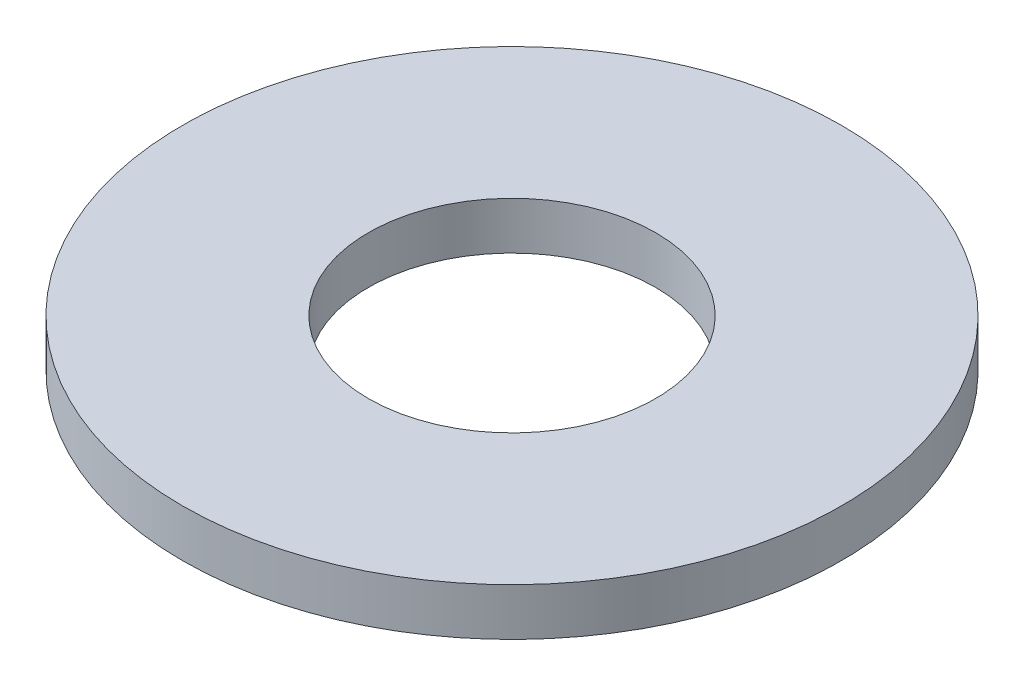
SolidWorks part; units mm, degrees
ref_plane "Front Plane" through (0, 0, 0) normal (0, 0, 1) x (1, 0, 0)
ref_plane "Top Plane" through (0, 0, 0) normal (0, 1, 0) x (1, 0, 0)
ref_plane "Right Plane" through (0, 0, 0) normal (1, 0, 0) x (0, 0, -1)
sketch "Sketch1" plane through (0, 0, 0) normal (0, 1, 0) x (1, 0, 0)
  circle A0 centre (0, 0) radius 3.175
  dimension "OD" = 6.35
extrude "Boss-Extrude1" add sketch "Sketch1" along normal blind 0.4572
sketch "Sketch5" plane through (0, 0.4572, 0) normal (0, 1, 0) x (-1, 0, 0)
  circle A0 centre (0, 0) radius 1.3843
  dimension "ID" = 2.7686
extrude "Cut-Extrude1" cut sketch "Sketch5" against normal through all
